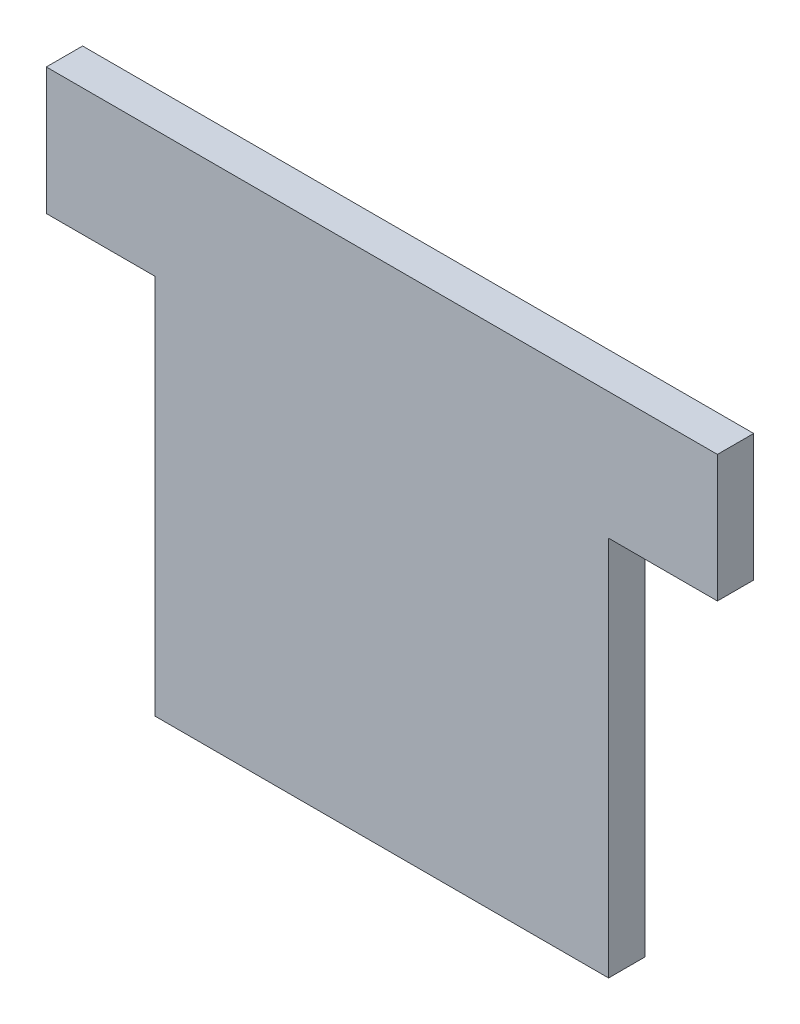
SolidWorks part; units mm, degrees
ref_plane "Ebene vorne" through (0, 0, 0) normal (0, 0, 1) x (1, 0, 0)
ref_plane "Ebene oben" through (0, 0, 0) normal (0, 1, 0) x (1, 0, 0)
ref_plane "Ebene rechts" through (0, 0, 0) normal (1, 0, 0) x (0, 0, -1)
sketch "Skizze1" plane through (0, 0, 0) normal (0, 0, 1) x (1, 0, 0)
  line L0 (0, 0) -> (0, -21)
  line L1 (0, -21) -> (25, -21)
  line L2 (25, -21) -> (25, 0)
  line L3 (25, 0) -> (31, 0)
  line L4 (31, 0) -> (31, 7)
  line L5 (31, 7) -> (-6, 7)
  line L6 (-6, 7) -> (-6, 0)
  line L7 (-6, 0) -> (0, 0)
  dimension "D1" = 25
  dimension "D2" = 28
  dimension "D3" = 6
  dimension "D4" = 7
extrude "Aufsatz-Linear austragen1" add sketch "Skizze1" along normal blind 2
